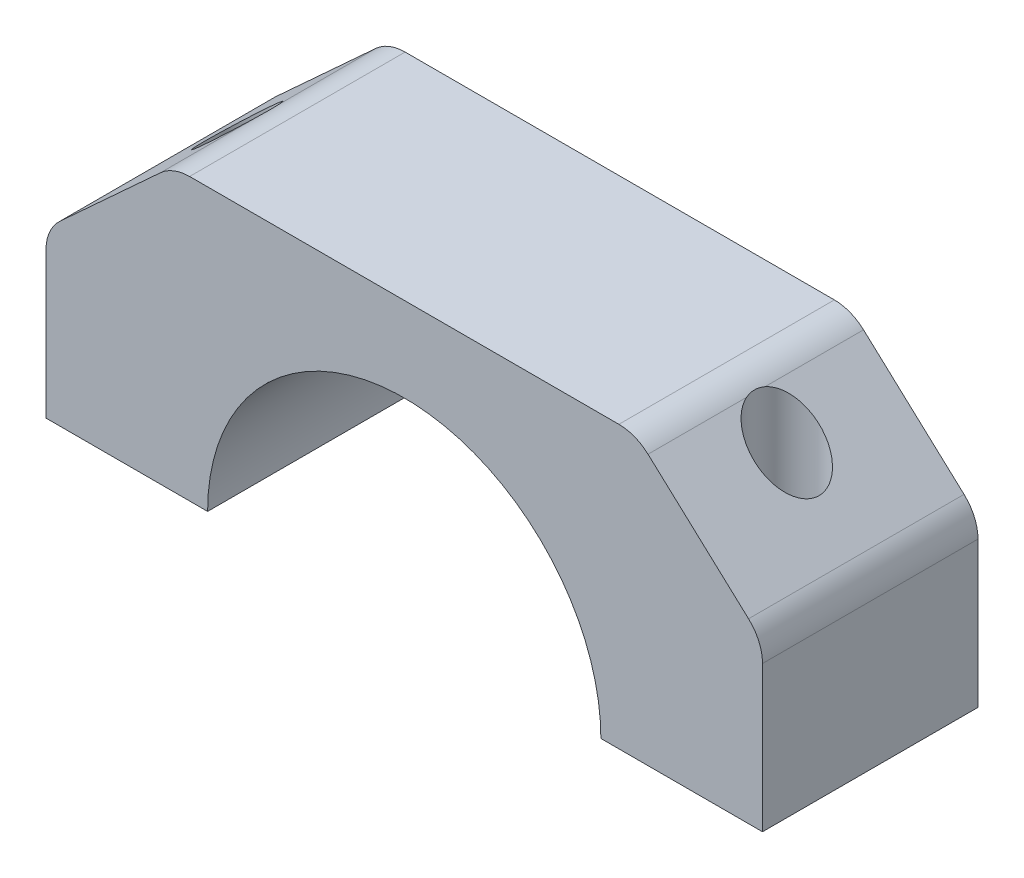
SolidWorks part; units mm, degrees
ref_plane "Front Plane" through (0, 0, 0) normal (0, 0, 1) x (1, 0, 0)
ref_plane "Top Plane" through (0, 0, 0) normal (0, 1, 0) x (1, 0, 0)
ref_plane "Right Plane" through (0, 0, 0) normal (1, 0, 0) x (0, 0, -1)
sketch "草图1" plane through (0, 0, 0) normal (0, 0, 1) x (1, 0, 0)
  line L0 (-33.25, 0) -> (-18.25, 0)
  line L1 (-33.25, 0) -> (-33.25, 13.5275)
  line L2 (-31.9544, 16.4747) -> (-22.6246, 25.0356)
  line L3 (-19.9203, 26.0884) -> (19.9203, 26.0884)
  line L4 (22.6246, 25.0356) -> (31.9544, 16.4747)
  line L5 (33.25, 13.5275) -> (33.25, 0)
  line L6 (18.25, 0) -> (33.25, 0)
  arc A1 (18.25, 0) -> (-18.25, 0) centre (0, 0) ccw
  arc A3 (31.9544, 16.4747) -> (33.25, 13.5275) centre (29.25, 13.5275) cw
  arc A4 (19.9203, 26.0884) -> (22.6246, 25.0356) centre (19.9203, 22.0884) cw
  arc A5 (-33.25, 13.5275) -> (-31.9544, 16.4747) centre (-29.25, 13.5275) cw
  arc A6 (-22.6246, 25.0356) -> (-19.9203, 26.0884) centre (-19.9203, 22.0884) cw
  dimension "D1" = 36.5
  dimension "D2" = 15
  dimension "D3" = 4
extrude "凸台-拉伸1" add sketch "草图1" along normal blind 20
sketch "草图2" plane through (0, 26.0884, 0) normal (0, 1, 0) x (1, 0, 0)
  line L0 (-50.7601, -10) -> (34.6433, -10) construction
  line L1 (19.9203, 0) -> (-19.9203, 0) construction
  line L2 (0, 9.6014) -> (0, -29.6735) construction
  circle A0 centre (-25.5, -10) radius 3
  circle A1 centre (25.5, -10) radius 3
  dimension "D4" = 6
  dimension "D1" = 10
  dimension "D2" = 25.5
  dimension "D3" = 25.5
extrude "切除-拉伸1" cut sketch "草图2" against normal blind 20
sketch "草图3" plane through (0, 26.0884, 0) normal (0, 1, 0) x (1, 0, 0)
  circle A0 centre (25.5, -10) radius 1.75
  circle A1 centre (-25.5, -10) radius 1.75
  dimension "D1" = 3.5
  dimension "D2" = 3.5
extrude "切除-拉伸2" cut sketch "草图3" against normal through all
